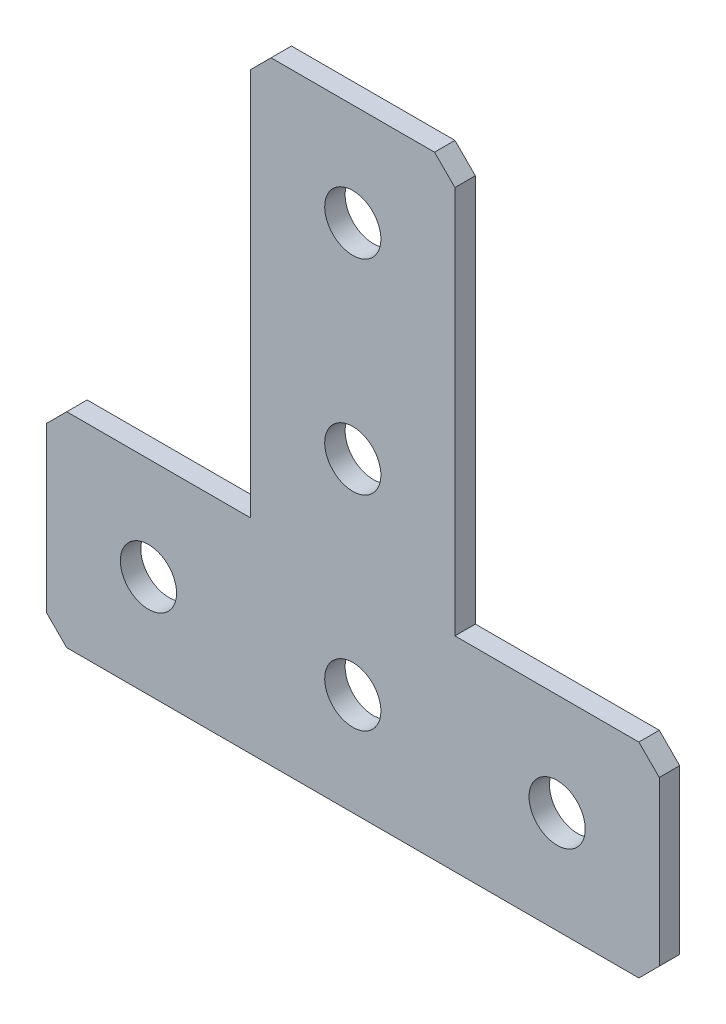
SolidWorks part; units mm, degrees
material "Простая углеродистая сталь"
ref_plane "Спереди(Плоскость XY)" through (0, 0, 0) normal (0, 0, 1) x (1, 0, 0)
ref_plane "Сверху(Плоскость XZ)" through (0, 0, 0) normal (0, 1, 0) x (1, 0, 0)
ref_plane "Справа(Плоскость ZY)" through (0, 0, 0) normal (1, 0, 0) x (0, 0, -1)
sketch "Эскиз1" plane through (0, 0, 0) normal (0, 0, -1) x (1, 0, 0)
  line L0 (0, 0) -> (0, 60) construction
  line L1 (-30, 60) -> (30, 60)
  line L2 (30, 60) -> (30, 40)
  line L3 (30, 40) -> (10, 40)
  line L4 (10, 40) -> (10, 0)
  line L5 (10, 0) -> (-10, 0)
  line L6 (-30, 60) -> (-30, 40)
  line L7 (-30, 40) -> (-10, 40)
  line L8 (-10, 40) -> (-10, 0)
  line L10 (-30, 50) -> (30, 50) construction
  dimension "D1" = 60
  dimension "D3" = 20
extrude "Бобышка-Вытянуть1" add sketch "Эскиз1" along normal blind 2
hole_wizard "Отверстие с зазором M51" positions "Эскиз2" profile "Эскиз3" hole size "M5" standard "DIN" end condition through all
sketch "Эскиз2" plane through (0, 0, -2) normal (0, 0, -1) x (1, 0, 0)
  line L6 (0, 0) -> (0, 60) construction
  line L7 (30, 60) -> (-30, 60) construction
  line L9 (-30, 50) -> (30, 50) construction
  line L10 (-30, 60) -> (-30, 40) construction
  line L11 (30, 40) -> (30, 60) construction
  point P38 (0, 50)
  point P40 (-20, 50)
  point P42 (20, 50)
  point P44 (0, 30)
  point P46 (0, 10)
  dimension "D1" = 20
  dimension "D2" = 20
  dimension "D3" = 20
  dimension "D4" = 20
sketch "Эскиз3" plane through (0, -10, -2) normal (1, 0, 0) x (0, 1, 0)
  line L0 (0, 0) -> (0, 2)
  line L1 (0, 2) -> (2.75, 2)
  line L2 (2.75, 2) -> (2.75, 0)
  line L5 (2.75, 0) -> (0, 0)
  line L11 (0, -6.35) -> (0, 107.95) construction
  dimension "Диаметр сквозного отверстия" = 5.5
  dimension "Глубина сквозного отверстия" = 2
chamfer "Фаска1" distance 2 angle 45 6 edges at (10, 0, -1) (30, -40, -1) (30, -60, -1) (-30, -60, -1) (-30, -40, -1) (-10, 0, -1)
